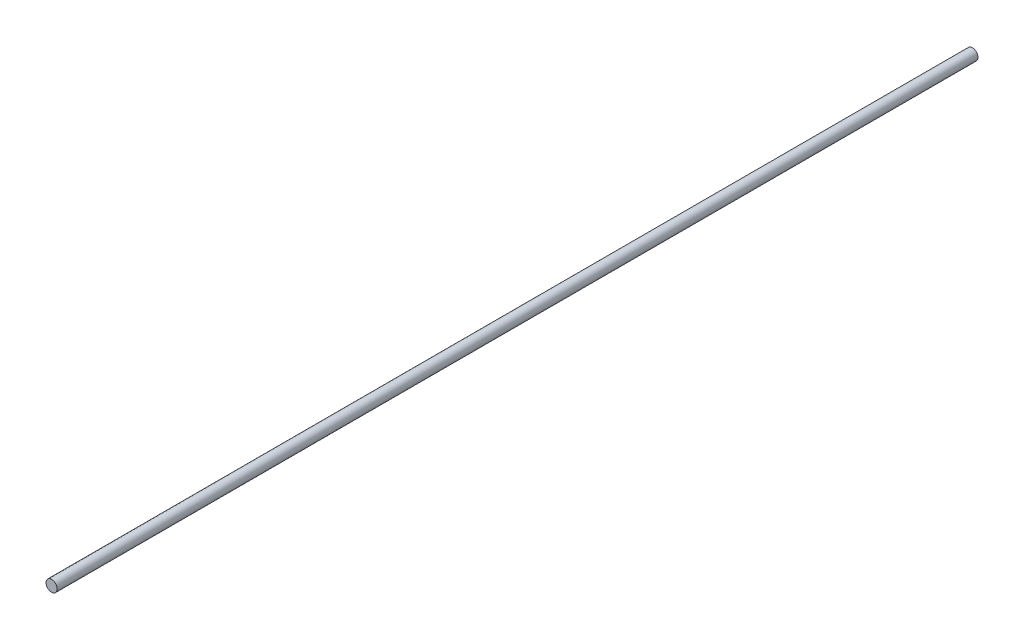
SolidWorks part; units mm, degrees
material "Plain Carbon Steel"
ref_plane "Front Plane" through (0, 0, 0) normal (0, 0, 1) x (1, 0, 0)
ref_plane "Top Plane" through (0, 0, 0) normal (0, 1, 0) x (1, 0, 0)
ref_plane "Right Plane" through (0, 0, 0) normal (1, 0, 0) x (0, 0, -1)
sketch "Sketch1" plane through (0, 0, 0) normal (0, 0, 1) x (1, 0, 0)
  circle A0 centre (0, 0) radius 2
  dimension "D1" = 4
extrude "Boss-Extrude1" add sketch "Sketch1" along normal blind 330
cosmetic thread "Cosmetic Thread1" parameters "D2"=3.22
